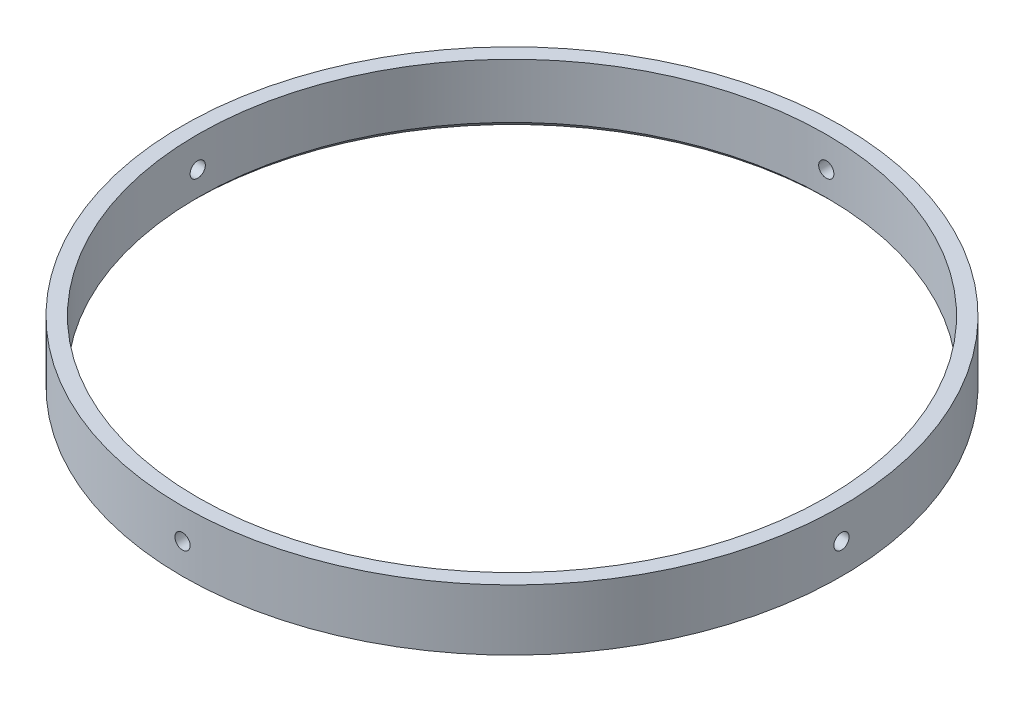
SolidWorks part; units mm, degrees
ref_plane "Front Plane" through (0, 0, 0) normal (0, 0, 1) x (1, 0, 0)
ref_plane "Top Plane" through (0, 0, 0) normal (0, 1, 0) x (1, 0, 0)
ref_plane "Right Plane" through (0, 0, 0) normal (1, 0, 0) x (0, 0, -1)
sketch "Sketch1" plane through (0, 0, 0) normal (0, 1, 0) x (1, 0, 0)
  circle A0 centre (0, 0) radius 68.834
  circle A1 centre (0, 0) radius 65.659
  dimension "D1" = 131.318
  dimension "D2" = 3.175
extrude "Boss-Extrude1" add sketch "Sketch1" along normal blind 12.7
sketch "Sketch2" plane through (0, 0, 0) normal (0, 0, 1) x (1, 0, 0)
  line L0 (0, 0) -> (0, 12.7) construction
  line L1 (65.659, 12.7) -> (-65.659, 12.7) construction
  circle A0 centre (0, 6.35) radius 1.5875
  dimension "D1" = 3.175
extrude "Cut-Extrude1" cut sketch "Sketch2" against normal up to surface (68.8157 mm away)
pattern_circular "CirPattern1" count 4 over 360 about axis through (0, 12.7, 0) along (0, -1, 0) of "Cut-Extrude1"
chamfer "Chamfer1" distance 1.27 angle 45 1 edges at (0, 0, 65.659)
